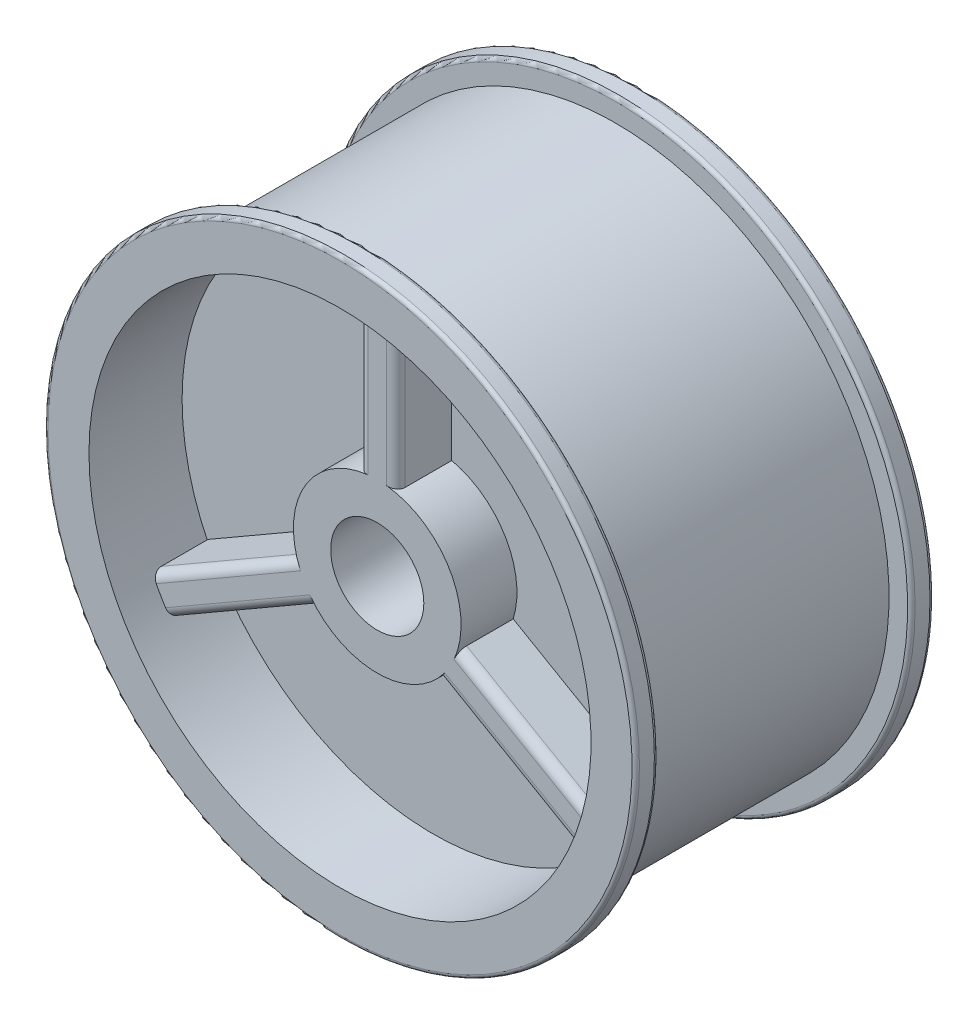
SolidWorks part; units mm, degrees
material "ABS"
ref_plane "Front Plane" through (0, 0, 0) normal (0, 0, 1) x (1, 0, 0)
ref_plane "Top Plane" through (0, 0, 0) normal (0, 1, 0) x (1, 0, 0)
ref_plane "Right Plane" through (0, 0, 0) normal (1, 0, 0) x (0, 0, -1)
sketch "Sketch3" plane through (0, 0, 0) normal (1, 0, 0) x (0, 0, -1)
  line L0 (0, 0) -> (0, 160) construction
  line L1 (0, 80) -> (-40, 80) construction
  line L2 (-40, 158.392) -> (-40, 147.392)
  line L9 (-40, 147.392) -> (-15, 147.392)
  line L10 (-15, 147.392) -> (-15, 80)
  line L11 (-15, 80) -> (0, 80)
  line L12 (-34, 158.392) -> (-34, 153.392)
  line L14 (-34, 153.392) -> (34, 153.392)
  line L21 (-39, 159.392) -> (-35, 159.392)
  line L22 (-40, 159.392) -> (-40, 147.392) construction
  line L23 (-9, 153.392) -> (-9, 86) construction
  line L24 (-9, 86) -> (0, 86) construction
  line L25 (-34, 153.392) -> (-9, 153.392) construction
  line L26 (-34, 159.392) -> (-34, 153.392) construction
  line L27 (15, 80) -> (0, 80)
  line L28 (15, 147.392) -> (15, 80)
  line L29 (40, 147.392) -> (15, 147.392)
  line L30 (39, 159.392) -> (35, 159.392)
  line L31 (34, 158.392) -> (34, 153.392)
  line L32 (40, 158.392) -> (40, 147.392)
  arc A0 (-40, 158.392) -> (-39, 159.392) centre (-39, 158.392) cw
  arc A1 (-34, 158.392) -> (-35, 159.392) centre (-35, 158.392) ccw
  arc A2 (34, 158.392) -> (35, 159.392) centre (35, 158.392) cw
  arc A3 (40, 158.392) -> (39, 159.392) centre (39, 158.392) ccw
  point P18 (-40, 159.392)
  point P26 (0, 153.392)
  point P32 (40, 159.392)
  dimension "D4" = 12
  dimension "D7" = 6
  dimension "D6" = 1
  dimension "D1" = 40
  dimension "D2" = 160
  dimension "D3" = 30
  dimension "D5" = 6
revolve "Revolve1" add sketch "Sketch3" angle 360 about L1
sketch "Sketch4" plane through (0, 0, 0) normal (0, 0, 1) x (1, 0, 0)
  line L0 (0, 94) -> (0, 147.392) construction
  line L1 (-5, 101.9374) -> (-5, 146.9224)
  line L2 (5, 101.9374) -> (5, 146.9224)
  line L3 (16.4984, 64.7012) -> (55.4565, 42.2087)
  line L4 (21.4984, 73.3614) -> (60.4565, 50.869)
  line L5 (-21.4984, 73.3614) -> (-60.4565, 50.869)
  line L6 (-16.4984, 64.7012) -> (-55.4565, 42.2087)
  line L7 (0, 80) -> (5, 101.9374) construction
  circle A0 centre (0, 80) radius 12.5
  arc A2 (-5, 101.9374) -> (-21.4984, 73.3614) centre (0, 80) ccw
  circle A3 centre (0, 80) radius 67.392 construction
  arc A4 (-5, 146.9224) -> (5, 146.9224) centre (0, 80) cw
  arc A5 (60.4565, 50.869) -> (55.4565, 42.2087) centre (0, 80) cw
  arc A6 (-55.4565, 42.2087) -> (-60.4565, 50.869) centre (0, 80) cw
  circle A7 centre (0, 80) radius 22.5 construction
  arc A8 (-16.4984, 64.7012) -> (16.4984, 64.7012) centre (0, 80) ccw
  arc A9 (21.4984, 73.3614) -> (5, 101.9374) centre (0, 80) ccw
  point P4 (0, 0)
  point P13 (0, 0)
  dimension "D1" = 25
  dimension "D2" = 10
  dimension "D5" = 44.9849
  dimension "D3" = 5
  dimension "D4" = 3
extrude "Boss-Extrude1" add sketch "Sketch4" along normal mid plane 60
sketch "Sketch6" plane through (0, 0, 30) normal (0, 0, 1) x (1, 0, 0)
  circle A0 centre (0, 80) radius 12.5
  dimension "D1" = 25
extrude "Cut-Extrude1" cut sketch "Sketch6" against normal through all
fillet "Fillet1" radius 2.5 12 edges at (5, 124.4299, 30) (-5, 124.4299, 30) (35.9774, 53.4549, -30) (40.9774, 62.1152, -30) (-5, 124.4299, -30) (5, 124.4299, -30) (-40.9774, 62.1152, -30) (-35.9774, 53.4549, -30) (40.9774, 62.1152, 30) (35.9774, 53.4549, 30) (-35.9774, 53.4549, 30) (-40.9774, 62.1152, 30)
scale "Scale1" scale about centroid uniform scaling yes scale factor 0.5
equation "\"shaft hole diameter\"= 12mm"
